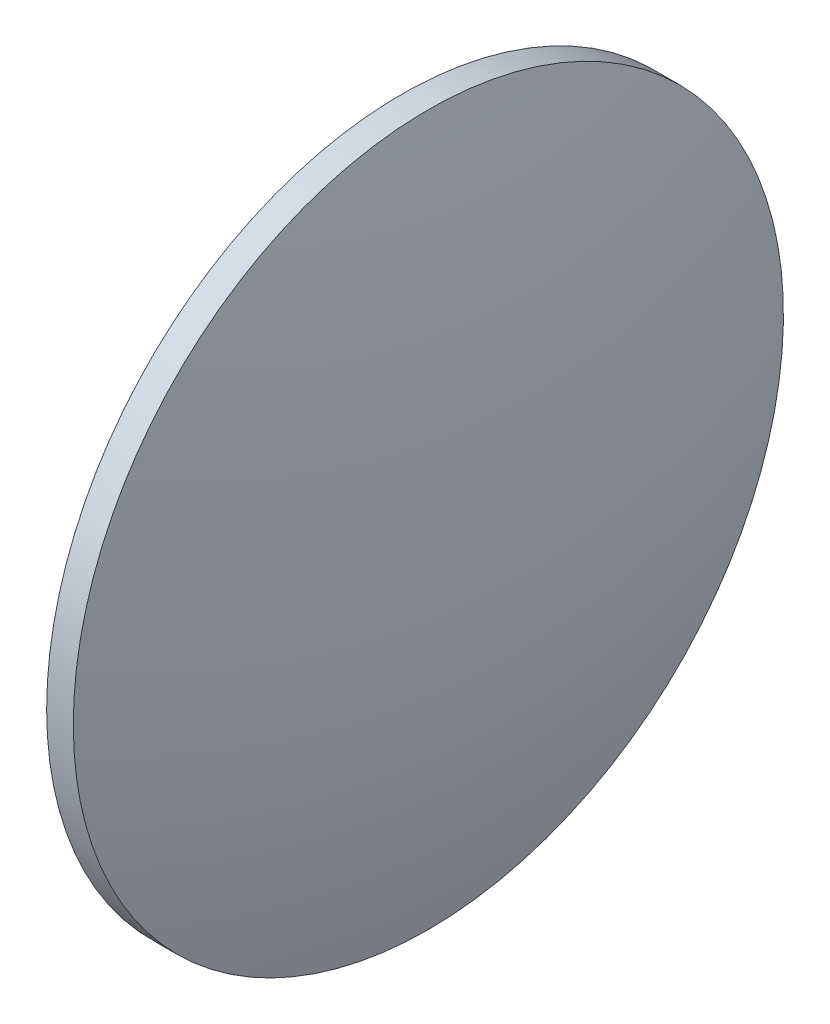
SolidWorks part; units mm, degrees
ref_plane "前视基准面" through (0, 0, 0) normal (0, 0, 1) x (1, 0, 0)
ref_plane "上视基准面" through (0, 0, 0) normal (0, 1, 0) x (1, 0, 0)
ref_plane "右视基准面" through (0, 0, 0) normal (1, 0, 0) x (0, 0, -1)
sketch "草图1" plane through (0, 0, 0) normal (0, 0, 1) x (1, 0, 0)
  line L0 (217.9946, 130.4671) -> (258.5717, 130.4671) construction
  line L1 (225.9491, 130.4671) -> (225.9491, 170.4671)
  line L2 (225.9491, 170.4671) -> (228.9491, 170.4671)
  line L3 (234.1991, 130.4671) -> (225.9491, 130.4671)
  arc A0 (234.1991, 130.4671) -> (228.9491, 170.4671) centre (79.1931, 130.4671) ccw
revolve "旋转1" add sketch "草图1" angle 360 about L0
